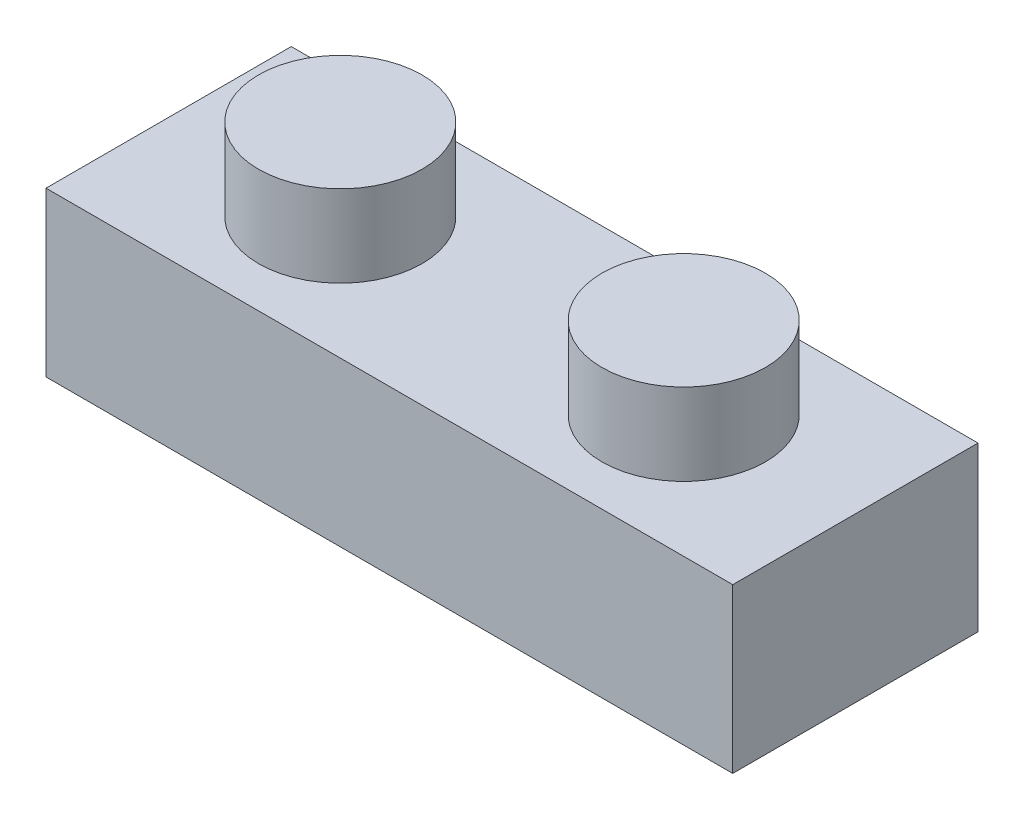
SolidWorks part; units mm, degrees
ref_plane "Front" through (0, 0, 0) normal (0, 0, 1) x (1, 0, 0)
ref_plane "Top" through (0, 0, 0) normal (0, 1, 0) x (1, 0, 0)
ref_plane "Right" through (0, 0, 0) normal (1, 0, 0) x (0, 0, -1)
sketch "草图1" plane through (0, 0, 0) normal (0, 1, 0) x (1, 0, 0)
  line L0 (0, 0) -> (42, 0) construction
  line L1 (42, 0) -> (42, -15) construction
  line L2 (0, 0) -> (42, 0)
  line L3 (42, 0) -> (42, -15)
  line L4 (42, -15) -> (0, -15)
  line L5 (0, -15) -> (0, 0)
extrude "凸台-拉伸1" add sketch "草图1" along normal blind 10
sketch "草图2" plane through (0, 10, 0) normal (0, 1, 0) x (1, 0, 0)
  line L0 (0, -7.5) -> (42, -7.5) construction
  line L1 (0, 0) -> (0, -15) construction
  line L2 (42, -15) -> (42, 0) construction
  line L3 (42, -7.5) -> (21, -7.5) construction
  line L4 (21, -7.5) -> (31.5, -7.5) construction
  line L5 (21, -7.5) -> (21, -12.1484) construction
  circle A0 centre (31.5, -7.5) radius 5
  circle A1 centre (10.5, -7.5) radius 5
extrude "凸台-拉伸2" add sketch "草图2" along normal blind 5
